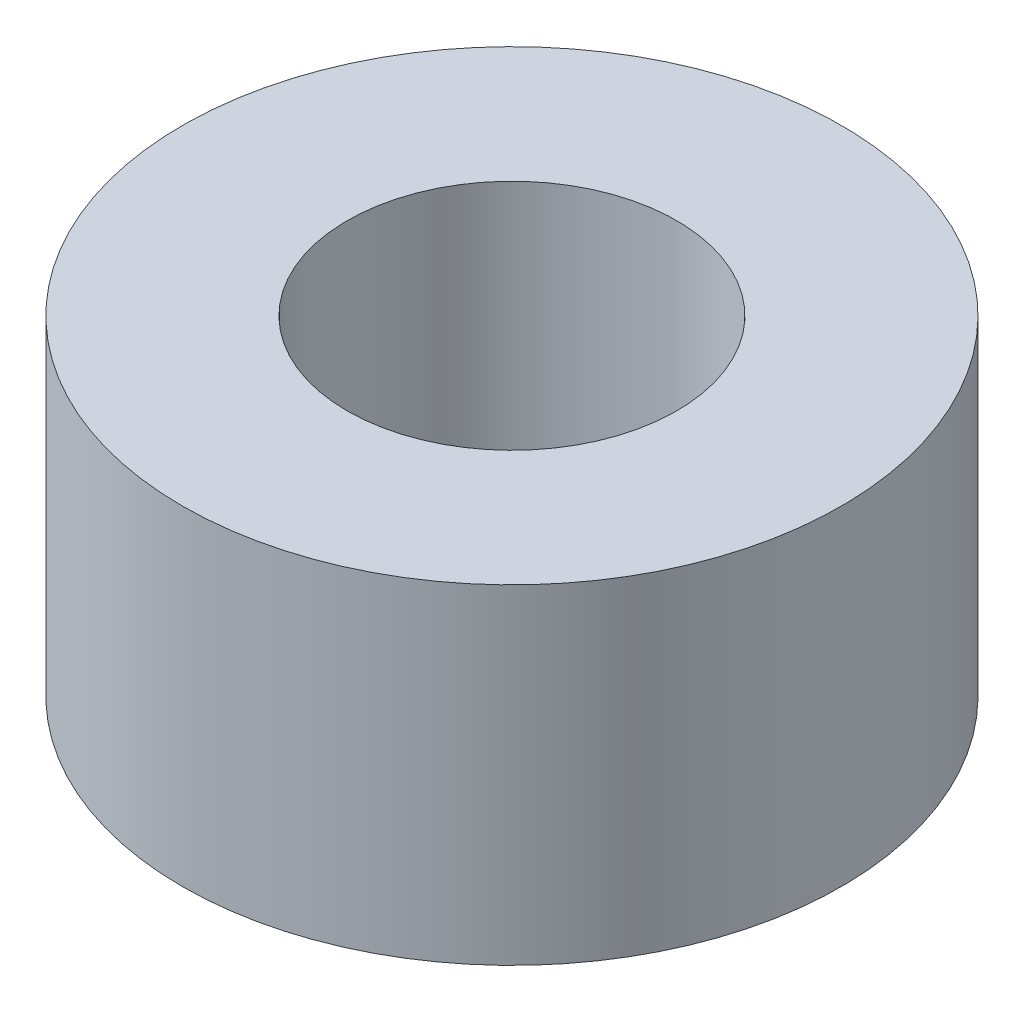
SolidWorks part; units mm, degrees
ref_plane "Front Plane" through (0, 0, 0) normal (0, 0, 1) x (1, 0, 0)
ref_plane "Top Plane" through (0, 0, 0) normal (0, 1, 0) x (1, 0, 0)
ref_plane "Right Plane" through (0, 0, 0) normal (1, 0, 0) x (0, 0, -1)
sketch "Sketch1" plane through (0, 0, 0) normal (0, 1, 0) x (1, 0, 0)
  circle A0 centre (0, 0) radius 3.175
  circle A1 centre (0, 0) radius 1.5875
  dimension "D1" = 6.35
  dimension "D2" = 3.175
extrude "Boss-Extrude1" add sketch "Sketch1" along normal blind 3.175
